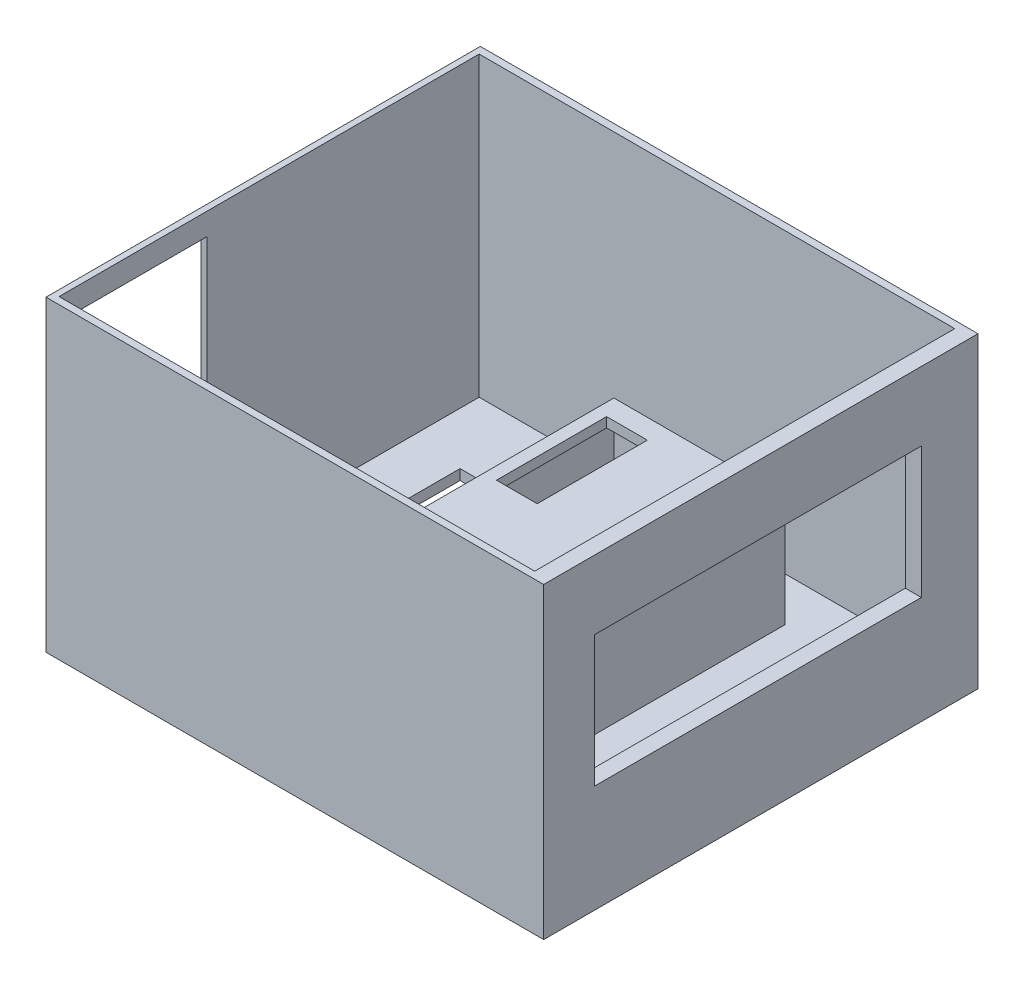
SolidWorks part; units mm, degrees
ref_plane "Front Plane" through (0, 0, 0) normal (0, 0, 1) x (1, 0, 0)
ref_plane "Top Plane" through (0, 0, 0) normal (0, 1, 0) x (1, 0, 0)
ref_plane "Right Plane" through (0, 0, 0) normal (1, 0, 0) x (0, 0, -1)
sketch "Sketch1" plane through (0, 0, 0) normal (0, 1, 0) x (1, 0, 0)
  line L1 (-72.9004, 81.3487) -> (71.0996, 81.3487)
  line L2 (-72.9004, 81.3487) -> (-72.9004, -44.3313)
  line L3 (-72.9004, -44.3313) -> (71.0996, -44.3313)
  line L4 (71.0996, 81.3487) -> (71.0996, -44.3313)
extrude "Boss-Extrude1" add sketch "Sketch1" along normal blind 3
sketch "Sketch2" plane through (0, 3, 0) normal (0, 1, 0) x (1, 0, 0)
  line L1 (-72.9004, 81.3487) -> (71.0996, 81.3487)
  line L2 (-72.9004, 81.3487) -> (-72.9004, -44.3313)
  line L3 (-72.9004, -44.3313) -> (71.0996, -44.3313)
  line L4 (71.0996, 81.3487) -> (71.0996, -44.3313)
  line L5 (-71.1533, 79.2527) -> (66.4736, 79.2527)
  line L6 (-71.1533, 79.2527) -> (-71.1533, -42.2955)
  line L7 (-71.1533, -42.2955) -> (66.4736, -42.2955)
  line L8 (66.4736, 79.2527) -> (66.4736, -42.2955)
extrude "Boss-Extrude2" add sketch "Sketch2" along normal blind 86
sketch "Sketch4" plane through (71.0996, 0, 0) normal (1, 0, 0) x (0, 0, -1)
  line L1 (64.9514, 69.0566) -> (-29.6059, 69.0566)
  line L2 (64.9514, 69.0566) -> (64.9514, 31.1026)
  line L3 (64.9514, 31.1026) -> (-29.6059, 31.1026)
  line L4 (-29.6059, 69.0566) -> (-29.6059, 31.1026)
extrude "Cut-Extrude1" cut sketch "Sketch4" against normal blind 20
sketch "Sketch6" plane through (-72.9004, 0, 0) normal (-1, 0, 0) x (0, 0, 1)
  line L1 (-0.5419, 6.9674) -> (39.2483, 6.9674)
  line L2 (-0.5419, 6.9674) -> (-0.5419, 82.619)
  line L3 (-0.5419, 82.619) -> (39.2483, 82.619)
  line L4 (39.2483, 6.9674) -> (39.2483, 82.619)
extrude "Cut-Extrude3" cut sketch "Sketch6" against normal blind 20
sketch "Sketch8" plane through (0, 3, 0) normal (0, 1, 0) x (1, 0, 0)
  line L1 (-19.4695, -25.2998) -> (30.0997, -25.2998)
  line L2 (-19.4695, -25.2998) -> (-19.4695, 66.5493)
  line L3 (-19.4695, 66.5493) -> (30.0997, 66.5493)
  line L4 (30.0997, -25.2998) -> (30.0997, 66.5493)
extrude "Boss-Extrude3" add sketch "Sketch8" along normal blind 32
sketch "Sketch7" plane through (0, 0, 0) normal (0, -1, 0) x (1, 0, 0)
  line L1 (-17.266, 22.9636) -> (27.734, 22.9636)
  line L2 (-17.266, 22.9636) -> (-17.266, -64.3464)
  line L3 (-17.266, -64.3464) -> (27.734, -64.3464)
  line L4 (27.734, 22.9636) -> (27.734, -64.3464)
  point P4 (5.234, 22.9636)
extrude "Cut-Extrude4" cut sketch "Sketch7" against normal blind 32.17
sketch "Sketch9" plane through (0, 32.17, 0) normal (0, -1, 0) x (1, 0, 0)
  line L1 (-4.0607, -60.8382) -> (-15.8579, -60.8382)
  line L2 (-4.0607, -60.8382) -> (-4.0607, -28.9718)
  line L3 (-4.0607, -28.9718) -> (-15.8579, -28.9718)
  line L4 (-15.8579, -60.8382) -> (-15.8579, -28.9718)
extrude "Cut-Extrude5" cut sketch "Sketch9" against normal blind 40
sketch "Sketch10" plane through (0, 32.17, 0) normal (0, -1, 0) x (1, 0, 0)
  line L1 (25.8116, -11.3729) -> (14.1238, -11.3729)
  line L2 (25.8116, -11.3729) -> (25.8116, 20.0569)
  line L3 (25.8116, 20.0569) -> (14.1238, 20.0569)
  line L4 (14.1238, -11.3729) -> (14.1238, 20.0569)
extrude "Cut-Extrude6" cut sketch "Sketch10" against normal blind 40
sketch "Sketch11" plane through (0, 0, 0) normal (0, -1, 0) x (1, 0, 0)
  line L1 (59.2163, -58.6112) -> (42.5661, -58.6112)
  line L2 (59.2163, -58.6112) -> (59.2163, 15.7034)
  line L3 (59.2163, 15.7034) -> (42.5661, 15.7034)
  line L4 (42.5661, -58.6112) -> (42.5661, 15.7034)
  line L5 (-31.5288, -58.6112) -> (-56.0347, -58.6112)
  line L6 (-31.5288, -58.6112) -> (-31.5288, 15.7034)
  line L7 (-31.5288, 15.7034) -> (-56.0347, 15.7034)
  line L8 (-56.0347, -58.6112) -> (-56.0347, 15.7034)
extrude "Cut-Extrude7" cut sketch "Sketch11" against normal blind 40
